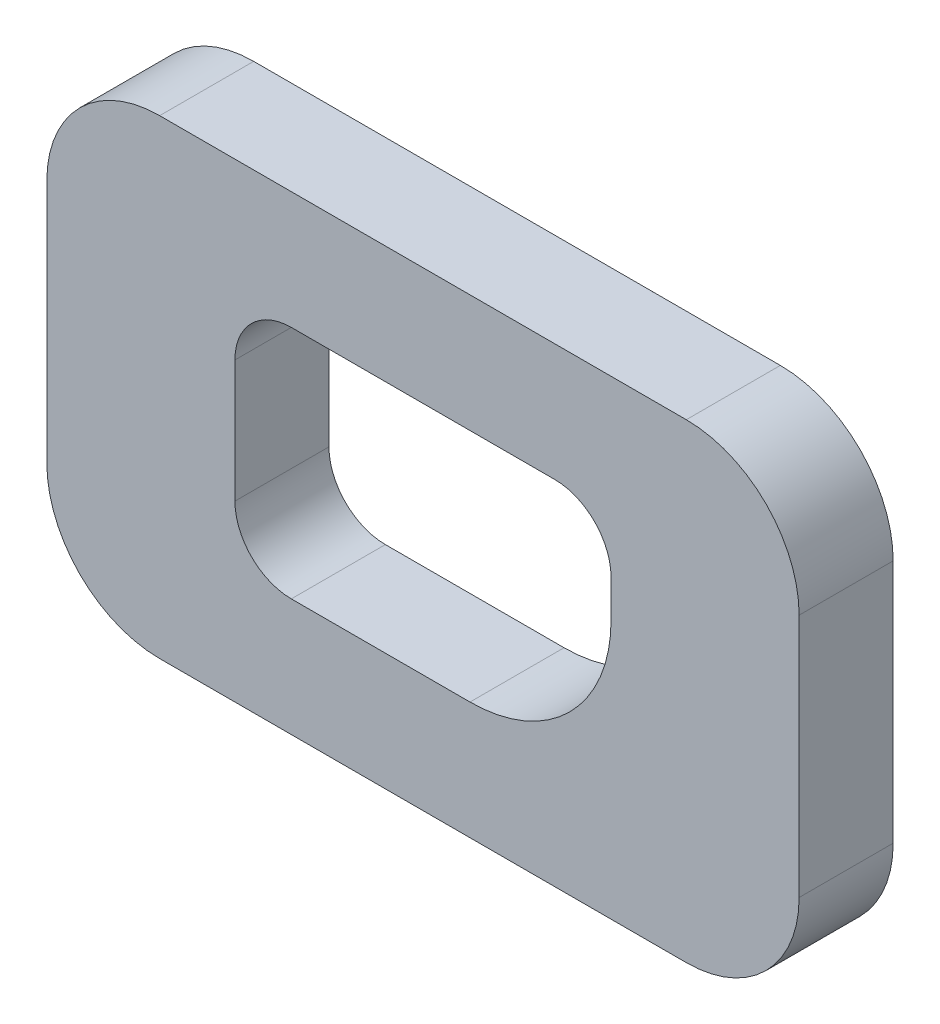
SolidWorks part; units mm, degrees
ref_plane "Plan de face" through (0, 0, 0) normal (0, 0, 1) x (1, 0, 0)
ref_plane "Plan de dessus" through (0, 0, 0) normal (0, 1, 0) x (1, 0, 0)
ref_plane "Plan de droite" through (0, 0, 0) normal (1, 0, 0) x (0, 0, -1)
sketch "Esquisse4" plane through (0, 0, 0) normal (0, 0, 1) x (1, 0, 0)
  line L1 (-14, -12.5) -> (5, -12.5)
  line L2 (-20, -6.5) -> (-20, 6.5)
  line L3 (-14, 12.5) -> (14, 12.5)
  line L4 (20, 2.5) -> (20, 6.5)
  line L5 (-20, -12.5) -> (20, 12.5) construction
  line L6 (-20, 12.5) -> (20, -12.5) construction
  line L7 (-28, -25) -> (28, -25)
  line L8 (-40, -13) -> (-40, 13)
  line L9 (-28, 25) -> (28, 25)
  line L10 (40, -13) -> (40, 13)
  line L11 (-40, -25) -> (40, 25) construction
  line L12 (-40, 25) -> (40, -25) construction
  arc A0 (28, 25) -> (40, 13) centre (28, 13) cw
  arc A1 (28, -25) -> (40, -13) centre (28, -13) ccw
  arc A2 (-28, -25) -> (-40, -13) centre (-28, -13) cw
  arc A3 (-40, 13) -> (-28, 25) centre (-28, 13) cw
  arc A4 (-20, 6.5) -> (-14, 12.5) centre (-14, 6.5) cw
  arc A5 (14, 12.5) -> (20, 6.5) centre (14, 6.5) cw
  arc A6 (5, -12.5) -> (20, 2.5) centre (5, 2.5) ccw
  arc A7 (-14, -12.5) -> (-20, -6.5) centre (-14, -6.5) cw
  point P0 (0, 0)
  point P6 (0, 0)
  dimension "D4" = 12
  dimension "D5" = 12
  dimension "D6" = 12
  dimension "D7" = 12
  dimension "D8" = 6
  dimension "D9" = 6
  dimension "D10" = 15
  dimension "D11" = 6
  dimension "D1" = 40
  dimension "D2" = 80
  dimension "D3" = 50
extrude "Boss.-Extru.5" add sketch "Esquisse4" along normal blind 10
